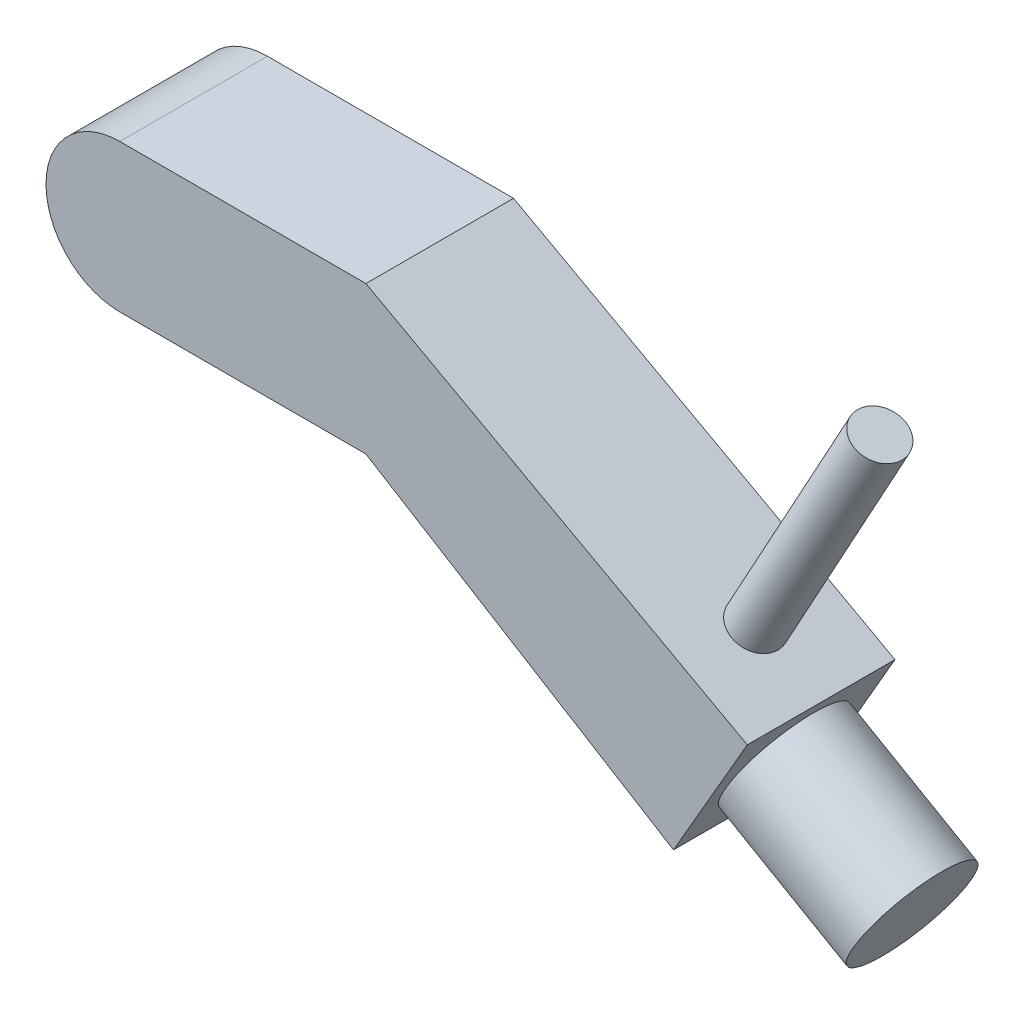
SolidWorks part; units mm, degrees
ref_plane "Front Plane" through (0, 0, 0) normal (0, 0, 1) x (1, 0, 0)
ref_plane "Top Plane" through (0, 0, 0) normal (0, 1, 0) x (1, 0, 0)
ref_plane "Right Plane" through (0, 0, 0) normal (1, 0, 0) x (0, 0, -1)
sketch "Sketch1" plane through (0, 0, 0) normal (0, 0, 1) x (1, 0, 0)
  line L0 (0, 0) -> (50, 0) construction
  line L1 (50, 0) -> (120, -40.4145) construction
  line L2 (127.5, -27.4241) -> (112.5, -53.4049)
  line L3 (0, 15) -> (0, -15) construction
  line L4 (0, 15) -> (50, 15)
  line L5 (0, -15) -> (50, -15)
  line L6 (50, -15) -> (112.5, -53.4049)
  line L7 (50, 15) -> (127.5, -27.4241)
  arc A1 (0, 15) -> (0, -15) centre (0, 0) ccw
  point P7 (120, -40.4145)
  point P10 (0, 0)
  dimension "D2" = 30
  dimension "D1" = 150
  dimension "D3" = 30
  dimension "D4" = 120
  dimension "D5" = 50
extrude "Boss-Extrude1" add sketch "Sketch1" along normal mid plane 30
sketch "Sketch4" plane through (107.5, -62.0652, 0) normal (0.866, -0.5, 0) x (0, 0, -1)
  line L0 (-15, 10) -> (15, 40) construction
  line L1 (15, 10) -> (15, 40) construction
  line L2 (-15, 40) -> (15, 40) construction
  circle A0 centre (0, 25) radius 12
  dimension "D1" = 24
extrude "Boss-Extrude2" add sketch "Sketch4" along normal blind 30
sketch "Sketch5" plane through (17.8462, 32.6013, 0) normal (0.4802, 0.8772, 0) x (0.8772, -0.4802, 0)
  line L0 (125.008, 0) -> (110.008, 0) construction
  line L1 (125.008, -15) -> (125.008, 15) construction
  circle A0 centre (110.008, 0) radius 5
  dimension "D2" = 10
  dimension "D1" = 15
extrude "Boss-Extrude3" add sketch "Sketch5" along normal up to surface (51.9861 mm away)
